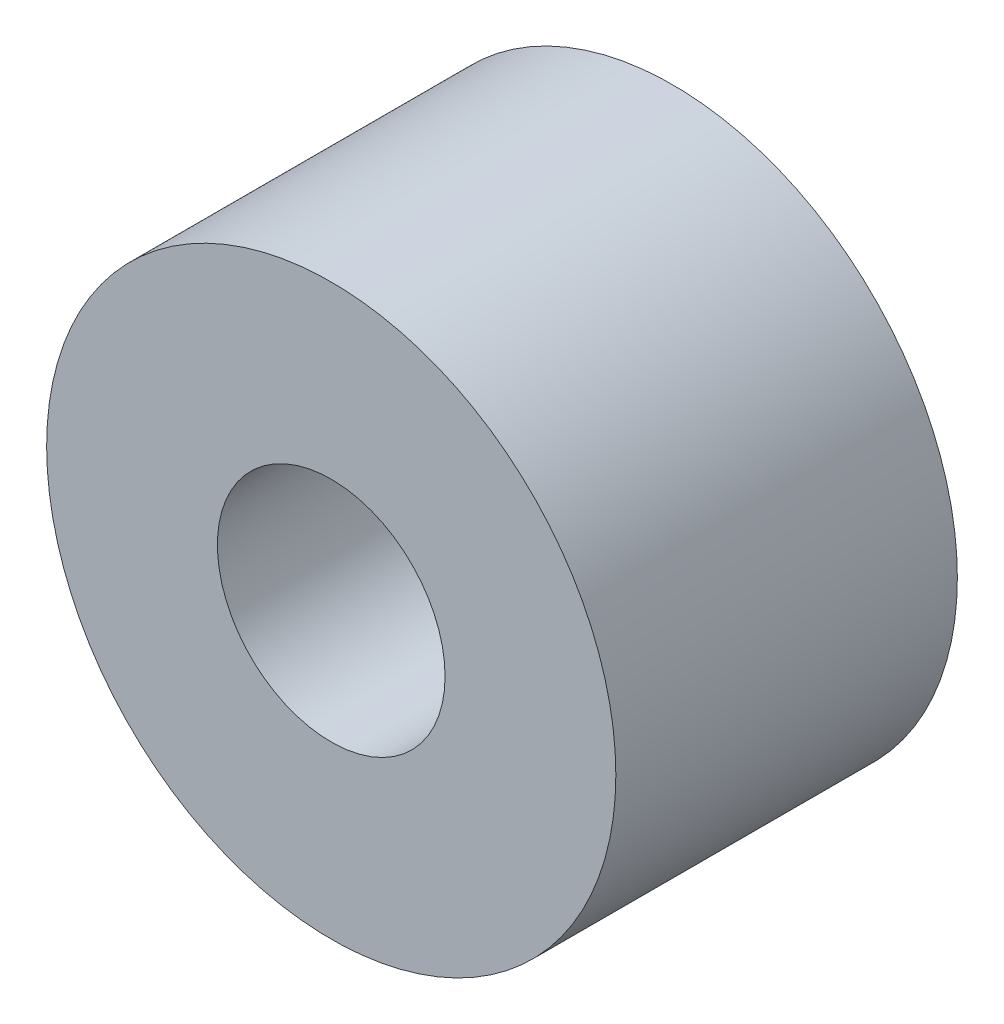
SolidWorks part; units mm, degrees
ref_plane "Ön Düzlem" through (0, 0, 0) normal (0, 0, 1) x (1, 0, 0)
ref_plane "Üst Düzlem" through (0, 0, 0) normal (0, 1, 0) x (1, 0, 0)
ref_plane "Sağ Düzlem" through (0, 0, 0) normal (1, 0, 0) x (0, 0, -1)
sketch "Çizim1" plane through (0, 0, 0) normal (0, 0, 1) x (1, 0, 0)
  circle A0 centre (0, 0) radius 2.5
  circle A1 centre (0, 0) radius 1
  dimension "D1" = 5
  dimension "D2" = 2
extrude "Yükseklik-Ekstrüzyon1" add sketch "Çizim1" along normal blind 3
